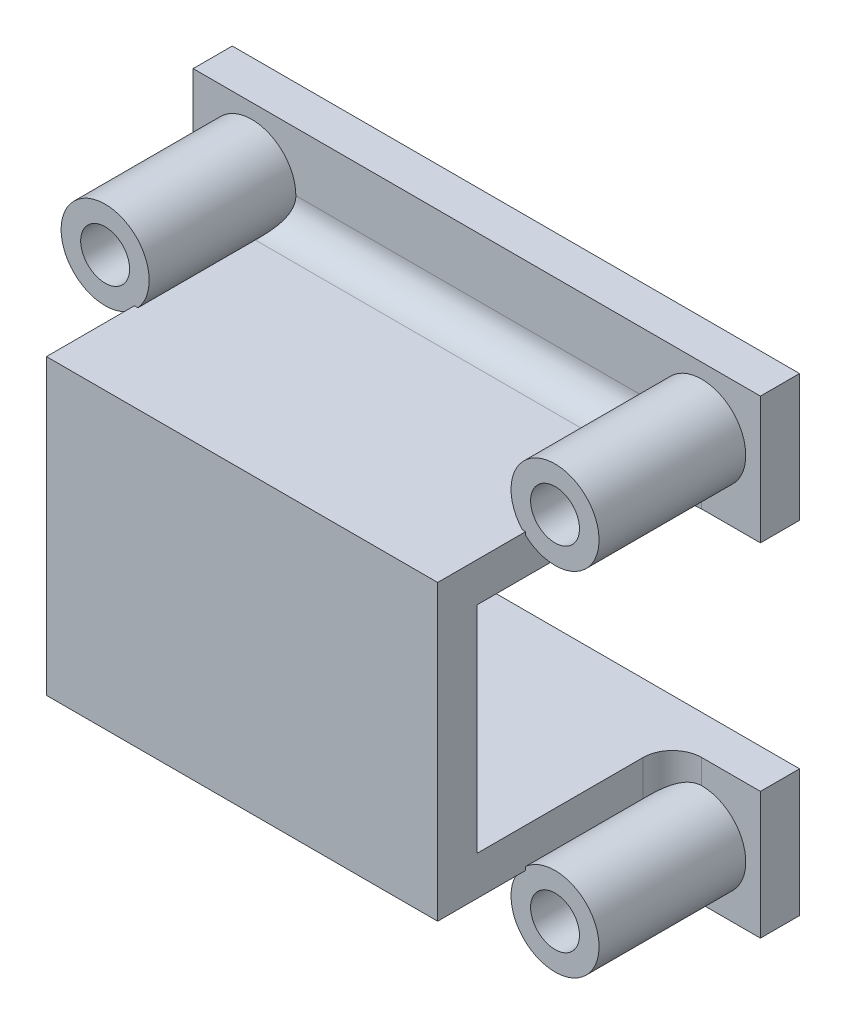
SolidWorks part; units mm, degrees
ref_plane "Alzado" through (0, 0, 0) normal (0, 0, 1) x (1, 0, 0)
ref_plane "Planta" through (0, 0, 0) normal (0, 1, 0) x (1, 0, 0)
ref_plane "Vista lateral" through (0, 0, 0) normal (1, 0, 0) x (0, 0, -1)
sketch "Croquis1" plane through (0, 0, 0) normal (0, 0, 1) x (1, 0, 0)
  line L1 (-14.5, 12) -> (14.5, 12)
  line L2 (-14.5, 12) -> (-14.5, -12)
  line L3 (-14.5, -12) -> (14.5, -12)
  line L4 (14.5, 12) -> (14.5, -12)
  line L5 (-14.5, 12) -> (14.5, -12) construction
  line L6 (-14.5, -12) -> (14.5, 12) construction
  point P0 (0, 0)
extrude "Saliente-Extruir1" add sketch "Croquis1" along normal blind 2
sketch "Croquis2" plane through (0, 0, 2) normal (0, 0, 1) x (1, 0, 0)
  line L0 (-14.5, 12) -> (-14.5, -12) construction
  line L1 (-14.5, 5.5) -> (14.5, 5.5)
  line L2 (-14.5, 5.5) -> (-14.5, -5.5)
  line L3 (-14.5, -5.5) -> (14.5, -5.5)
  line L4 (14.5, 5.5) -> (14.5, -5.5)
  line L5 (14.5, -12) -> (14.5, 12) construction
extrude "Cortar-Extruir1" cut sketch "Croquis2" against normal blind 2
sketch "Croquis3" plane through (0, 0, 2) normal (0, 0, 1) x (1, 0, 0)
  line L3 (-14.5, 12) -> (-14.5, 5.5) construction
  line L4 (14.5, 12) -> (-14.5, 12) construction
  circle A0 centre (-11.5, 9) radius 1.25
  point P6 (-14.5, 9.059)
  dimension "D1" = 3
  dimension "D2" = 3
extrude "Cortar-Extruir2" cut sketch "Croquis3" against normal blind 2
mirror "Simetría2" about plane through (0, 0, 0) normal (1, 0, 0) of "Cortar-Extruir2"
mirror "Simetría5" about plane through (0, 0, 0) normal (0, 1, 0) of "Simetría2", "Cortar-Extruir2"
sketch "Croquis4" plane through (0, 0, 2) normal (0, 0, 1) x (1, 0, 0)
  line L0 (14.5, 5.5) -> (-14.5, 5.5) construction
  line L1 (-10, 5.5) -> (10, 5.5)
  line L2 (-10, 5.5) -> (-10, 7.5)
  line L3 (-10, 7.5) -> (10, 7.5)
  line L4 (10, 5.5) -> (10, 7.5)
  line L5 (14.5, 5.5) -> (14.5, 12) construction
  line L8 (-14.5, 12) -> (-14.5, 5.5) construction
  point P6 (10, 6.5)
  dimension "D1" = 4.5
  dimension "D2" = 4.5
extrude "Saliente-Extruir2" add sketch "Croquis4" along normal blind 12
sketch "Croquis5" plane through (0, 5.5, 0) normal (0, -1, 0) x (-1, 0, 0)
  line L0 (-10, -14) -> (-10, -2) construction
  line L1 (10, -14) -> (-10, -14)
  line L2 (10, -14) -> (10, -12)
  line L3 (10, -12) -> (-10, -12)
  line L4 (-10, -14) -> (-10, -12)
  dimension "D1" = 10
sketch "Croquis6" plane through (0, 0, 2) normal (0, 0, 1) x (1, 0, 0)
  line L0 (-14.5, -5.5) -> (14.5, -5.5) construction
  line L1 (-10, -5.5) -> (10, -5.5)
  line L2 (-10, -5.5) -> (-10, -7.5)
  line L3 (-10, -7.5) -> (10, -7.5)
  line L4 (10, -5.5) -> (10, -7.5)
  line L7 (-14.5, -5.5) -> (-14.5, -12) construction
  line L8 (14.5, -12) -> (14.5, -5.5) construction
  dimension "D1" = 4.5
  dimension "D2" = 4.5
  dimension "D3" = 2
extrude "Saliente-Extruir4" add sketch "Croquis6" along normal blind 12
extrude "Saliente-Extruir5" add sketch "Croquis5" along normal up to surface (11 mm away) up to face at (0, -5.5, 4.5)
sketch "Croquis7" plane through (0, 0, 2) normal (0, 0, 1) x (1, 0, 0)
  circle A0 centre (-11.5, 9) radius 1.25
extrude "Extruir-Lámina1" add sketch "Croquis7" along normal blind 7.5 thin
mirror "Simetría8" about plane through (0, 0, 0) normal (1, 0, 0) of "Extruir-Lámina1"
mirror "Simetría10" about plane through (0, 0, 0) normal (0, 1, 0) of "Simetría8", "Extruir-Lámina1"
fillet "Redondeo1" radius 1.5 6 edges at (-10, -6.4115, 2) (0, -7.5, 2) (10, -6.4115, 2) (-10, 6.4115, 2) (10, 6.4115, 2) (0, 7.5, 2)
